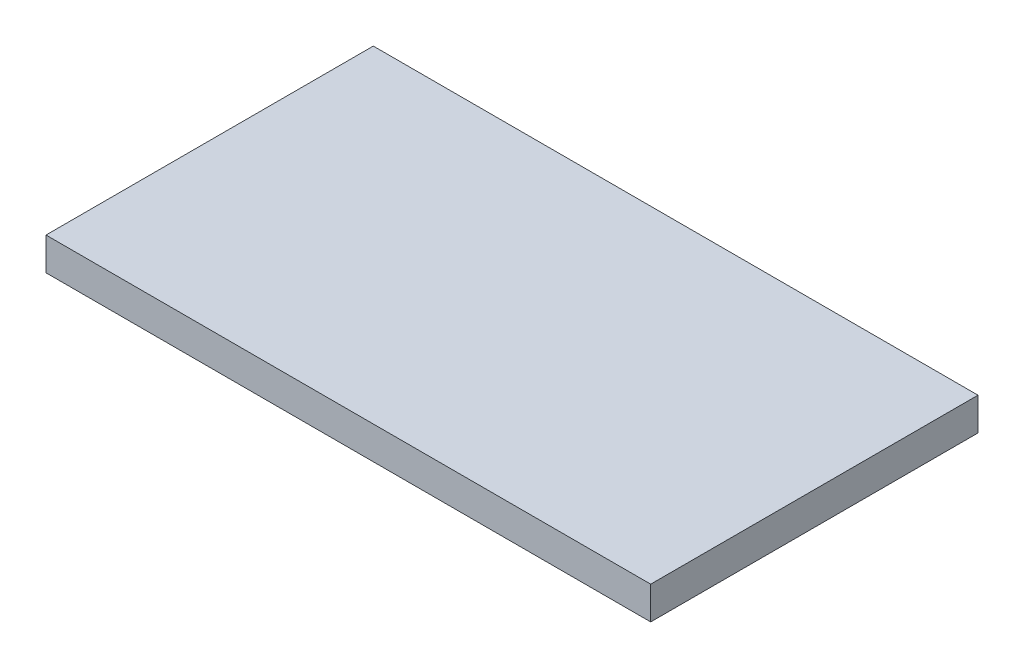
SolidWorks part; units mm, degrees
ref_plane "Front Plane" through (0, 0, 0) normal (0, 0, 1) x (1, 0, 0)
ref_plane "Top Plane" through (0, 0, 0) normal (0, 1, 0) x (1, 0, 0)
ref_plane "Right Plane" through (0, 0, 0) normal (1, 0, 0) x (0, 0, -1)
sketch "Sketch2" plane through (0, 0, 0) normal (0, 1, 0) x (1, 0, 0)
  line L1 (-92.375, -50) -> (92.375, -50)
  line L2 (-92.375, -50) -> (-92.375, 50)
  line L3 (-92.375, 50) -> (92.375, 50)
  line L4 (92.375, -50) -> (92.375, 50)
  line L5 (-92.375, -50) -> (92.375, 50) construction
  line L6 (-92.375, 50) -> (92.375, -50) construction
  point P0 (0, 0)
  dimension "D1" = 100
  dimension "D2" = 184.75
extrude "Boss-Extrude1" add sketch "Sketch2" along normal blind 10
